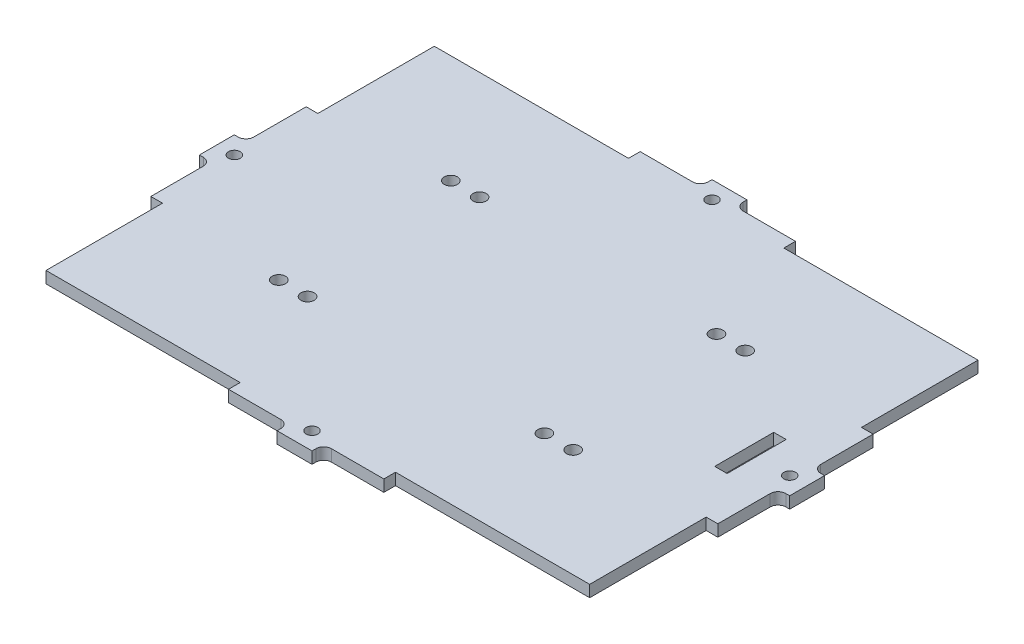
SolidWorks part; units mm, degrees
material "Acrylic (Medium-high impact)"
ref_plane "Plano frontal" through (0, 0, 0) normal (0, 0, 1) x (1, 0, 0)
ref_plane "Plano superior" through (0, 0, 0) normal (0, 1, 0) x (1, 0, 0)
ref_plane "Plano direito" through (0, 0, 0) normal (1, 0, 0) x (0, 0, -1)
sketch "Esboço1" plane through (0, 0, 0) normal (0, 1, 0) x (1, 0, 0)
  line L1 (-70, -50) -> (70, -50)
  line L2 (-70, -50) -> (-70, 50)
  line L3 (-70, 50) -> (70, 50)
  line L4 (70, -50) -> (70, 50)
  line L5 (-70, -50) -> (70, 50) construction
  line L6 (-70, 50) -> (70, -50) construction
  point P0 (0, 0)
  dimension "D1" = 140
  dimension "D2" = 100
extrude "Ressalto-extrusão1" add sketch "Esboço1" along normal mid plane 3
sketch "Esboço4" plane through (0, 1.5, 0) normal (0, 1, 0) x (1, 0, 0)
  line L5 (0, -1.65) -> (0, 1.65) construction
  line L21 (6.5, 53) -> (20, 53)
  line L26 (-4.5, 56) -> (4.5, 56)
  line L27 (-4.5, 56) -> (-4.5, 55)
  line L33 (-76, 4.5) -> (-76, -4.5)
  line L42 (70, 50) -> (-70, 50) construction
  line L43 (-20, 50) -> (20, 50)
  line L44 (-20, 50) -> (-20, 53)
  line L45 (-20, 53) -> (-6.5, 53)
  line L46 (20, 50) -> (20, 53)
  line L48 (4.5, 56) -> (4.5, 55)
  line L49 (-1.65, 0) -> (1.65, 0) construction
  line L50 (4.5, -56) -> (4.5, -55)
  line L51 (20, -50) -> (20, -53)
  line L52 (-20, -53) -> (-6.5, -53)
  line L53 (-20, -50) -> (-20, -53)
  line L54 (-20, -50) -> (20, -50)
  line L55 (-4.5, -56) -> (-4.5, -55)
  line L56 (-4.5, -56) -> (4.5, -56)
  line L57 (6.5, -53) -> (20, -53)
  line L58 (70, -50) -> (70, 50) construction
  line L59 (70, 20) -> (73, 20)
  line L60 (70, 20) -> (70, -20)
  line L61 (70, -20) -> (73, -20)
  line L62 (73, 20) -> (73, 6.5)
  line L63 (73, -6.5) -> (73, -20)
  line L64 (75, 4.5) -> (76, 4.5)
  line L66 (75, -4.5) -> (76, -4.5)
  line L67 (76, 4.5) -> (76, -4.5)
  line L77 (-75, -4.5) -> (-76, -4.5)
  line L91 (-75, 4.5) -> (-76, 4.5)
  line L92 (-73, -6.5) -> (-73, -20)
  line L93 (-73, 20) -> (-73, 6.5)
  line L94 (-70, -20) -> (-73, -20)
  line L95 (-70, 20) -> (-70, -20)
  line L96 (-70, 20) -> (-73, 20)
  circle A6 centre (0, 51.5) radius 1.5 construction
  arc A7 (6.5, 53) -> (4.5, 55) centre (6.5, 55) cw
  arc A8 (-4.5, 55) -> (-6.5, 53) centre (-6.5, 55) cw
  circle A9 centre (0, -51.5) radius 1.5 construction
  arc A10 (-4.5, -55) -> (-6.5, -53) centre (-6.5, -55) ccw
  arc A11 (6.5, -53) -> (4.5, -55) centre (6.5, -55) ccw
  arc A12 (73, -6.5) -> (75, -4.5) centre (75, -6.5) cw
  arc A13 (75, 4.5) -> (73, 6.5) centre (75, 6.5) cw
  arc A18 (-75, 4.5) -> (-73, 6.5) centre (-75, 6.5) ccw
  arc A19 (-73, -6.5) -> (-75, -4.5) centre (-75, -6.5) ccw
  point P16 (76, 0)
  point P20 (73, 4.5)
  point P21 (70, 0)
  point P36 (-73, 4.5)
  point P42 (0, 50)
  point P51 (4.5, 53)
  point P70 (4.5, -53)
  dimension "D2" = 9
  dimension "D6" = 2
  dimension "D8" = 3
  dimension "D9" = 3
  dimension "D11" = 2
  dimension "D3" = 40
  dimension "D4" = 9
  dimension "D5" = 3
  dimension "D10" = 3
extrude "Ressalto-extrusão2" add sketch "Esboço4" against normal through all
sketch "Esboço2" plane through (0, 1.5, 0) normal (0, 1, 0) x (1, 0, 0)
  line L27 (0, -1.65) -> (0, 1.65) construction
  line L32 (-20, -53) -> (-6.5, -53) construction
  line L51 (76, -4.5) -> (76, 4.5) construction
  line L90 (-4.5, -56) -> (4.5, -56) construction
  line L91 (-1.65, 0) -> (1.65, 0) construction
  circle A8 centre (0, -51.5) radius 1.5
  circle A9 centre (0, 51.5) radius 1.5
  circle A11 centre (71.5, 0) radius 1.5
  circle A14 centre (-71.5, 0) radius 1.5
  dimension "D1" = 3
  dimension "D2" = 3
  dimension "D3" = 3
extrude "Corte-extrusão1" cut sketch "Esboço2" against normal through all
sketch "Sketch1" plane through (0, 1.5, 0) normal (0, 1, 0) x (1, 0, 0)
  line L0 (-1.65, 0) -> (1.65, 0) construction
  line L1 (0, -1.65) -> (0, 1.65) construction
  circle A0 centre (30.5, -22.15) radius 1.7 construction
  circle A1 centre (30.5, -22.15) radius 1.7
  circle A2 centre (37.9, -22.15) radius 1.7 construction
  circle A3 centre (37.9, -22.15) radius 1.7
  circle A4 centre (37.9, 22.15) radius 1.7
  circle A5 centre (30.5, 22.15) radius 1.7
  circle A6 centre (-30.5, 22.15) radius 1.7
  circle A7 centre (-37.9, 22.15) radius 1.7
  circle A8 centre (-37.9, -22.15) radius 1.7
  circle A9 centre (-30.5, -22.15) radius 1.7
extrude "Cut-Extrude1" cut sketch "Sketch1" against normal through all both and the other way through all
sketch "Sketch2" plane through (0, 0, 0) normal (0, 1, 0) x (1, 0, 0)
  line L0 (59.8, 7.6) -> (63, 7.6)
  line L1 (59.9, 7.5) -> (62.9, 7.5) construction
  line L2 (59.9, 7.5) -> (59.9, -7.5) construction
  line L3 (59.9, -7.5) -> (62.9, -7.5) construction
  line L4 (62.9, 7.5) -> (62.9, -7.5) construction
  line L5 (63, 7.6) -> (63, -7.6)
  line L6 (59.8, -7.6) -> (63, -7.6)
  line L7 (59.8, 7.6) -> (59.8, -7.6)
  line L8 (70, 20) -> (70, 50) construction
  line L10 (42, 12.5) -> (67, 12.5) construction
  line L11 (42, 12.5) -> (42, -12.5) construction
  line L12 (42, -12.5) -> (67, -12.5) construction
  line L13 (67, 12.5) -> (67, -12.5) construction
  line L14 (48, 9) -> (53, 9) construction
  line L15 (48, 9) -> (48, -9) construction
  line L16 (48, -9) -> (53, -9) construction
  line L17 (53, 9) -> (53, -9) construction
  point P4 (62.9, 0)
  point P10 (63, 0)
  point P17 (59.8, 0)
  point P18 (42, 0)
  point P21 (48, 0)
  dimension "D1" = 15
  dimension "D2" = 3
  dimension "D4" = 5
  dimension "D5" = 25
  dimension "D6" = 4
  dimension "D7" = 25
  dimension "D8" = 6
  dimension "D9" = 18
  dimension "D10" = 3
  dimension "D3" = 0.1
extrude "Cut-Extrude3" cut sketch "Sketch2" against normal through all both and the other way through all
